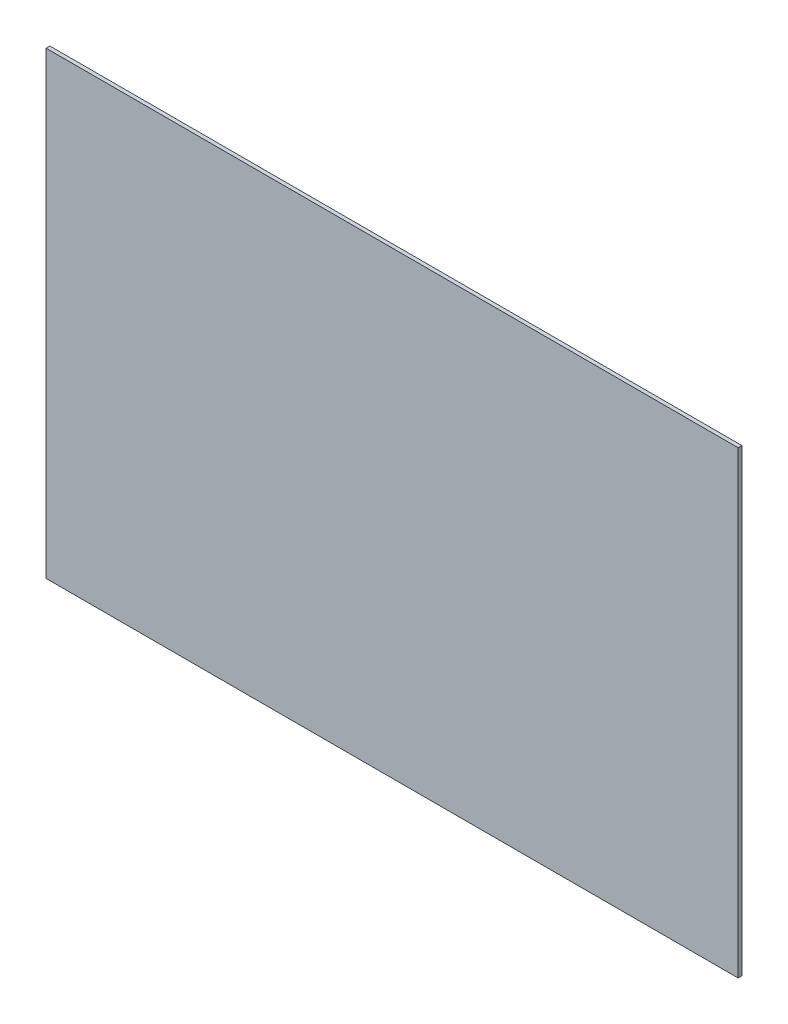
SolidWorks part; units mm, degrees
ref_plane "Plan de face" through (0, 0, 0) normal (0, 0, 1) x (1, 0, 0)
ref_plane "Plan de dessus" through (0, 0, 0) normal (0, 1, 0) x (1, 0, 0)
ref_plane "Plan de droite" through (0, 0, 0) normal (1, 0, 0) x (0, 0, -1)
sketch "Esquisse1" plane through (0, 0, 0) normal (0, 0, 1) x (1, 0, 0)
  line L1 (-201.9361, 140.9233) -> (348.0639, 140.9233)
  line L2 (-201.9361, 140.9233) -> (-201.9361, -224.0767)
  line L3 (-201.9361, -224.0767) -> (348.0639, -224.0767)
  line L4 (348.0639, 140.9233) -> (348.0639, -224.0767)
  dimension "D1" = 365
  dimension "D2" = 550
extrude "Boss.-Extru.1" add sketch "Esquisse1" along normal blind 3
